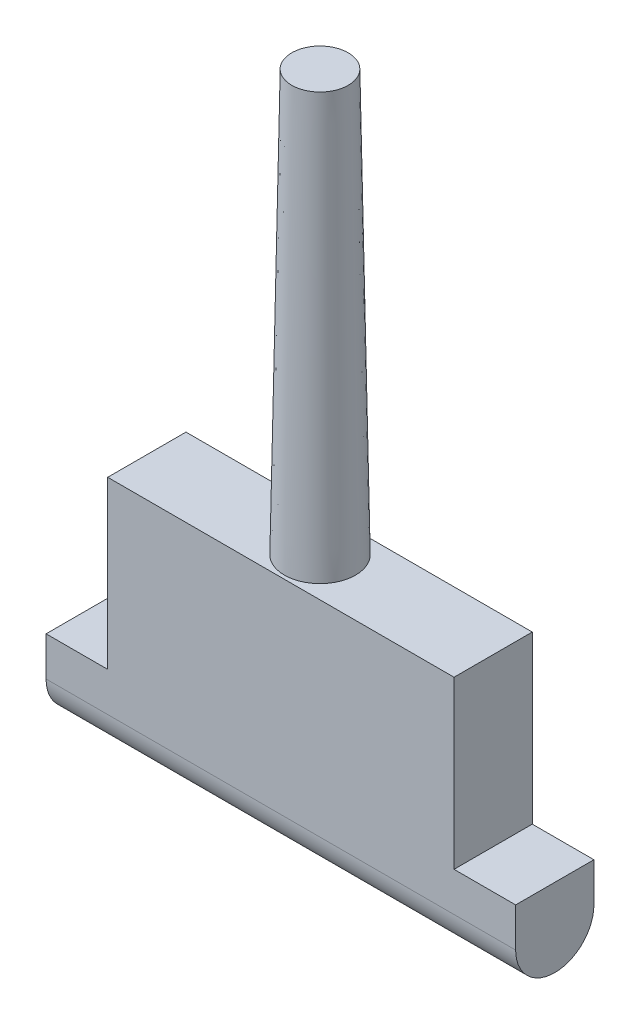
SolidWorks part; units mm, degrees
ref_plane "Front Plane" through (0, 0, 0) normal (0, 0, 1) x (1, 0, 0)
ref_plane "Top Plane" through (0, 0, 0) normal (0, 1, 0) x (1, 0, 0)
ref_plane "Right Plane" through (0, 0, 0) normal (1, 0, 0) x (0, 0, -1)
sketch "Sketch1" plane through (0, 0, 0) normal (1, 0, 0) x (0, 0, -1)
  line L0 (-3.175, 0) -> (-3.175, 3.175)
  line L1 (-3.175, 3.175) -> (3.175, 3.175)
  line L2 (3.175, 3.175) -> (3.175, 0)
  arc A0 (-3.175, 0) -> (3.175, 0) centre (0, 0) ccw
  dimension "D1" = 6.35
extrude "Boss-Extrude1" add sketch "Sketch1" along normal mid plane 38.1
sketch "Sketch2" plane through (0, 0, 0) normal (0, 1, 0) x (1, 0, 0)
  circle A0 centre (0, 0) radius 3.175
  dimension "D1" = 6.35
extrude "Boss-Extrude2" add sketch "Sketch2" along normal blind 50.8 draft 1
sketch "Sketch3" plane through (0, 0, 0) normal (0, 0, 1) x (1, 0, 0)
  line L0 (19.05, 3.175) -> (-19.05, 3.175) construction
  line L1 (-14.05, 3.175) -> (14.05, 3.175)
  line L2 (-14.05, 3.175) -> (-14.05, 16.675)
  line L3 (-14.05, 16.675) -> (14.05, 16.675)
  line L4 (14.05, 3.175) -> (14.05, 16.675)
  line L5 (-19.05, 3.175) -> (-19.05, 0) construction
  line L6 (19.05, 3.175) -> (19.05, 0) construction
  dimension "D1" = 13.5
  dimension "D2" = 5
  dimension "D3" = 5
extrude "Boss-Extrude3" add sketch "Sketch3" along normal mid plane 6.35
